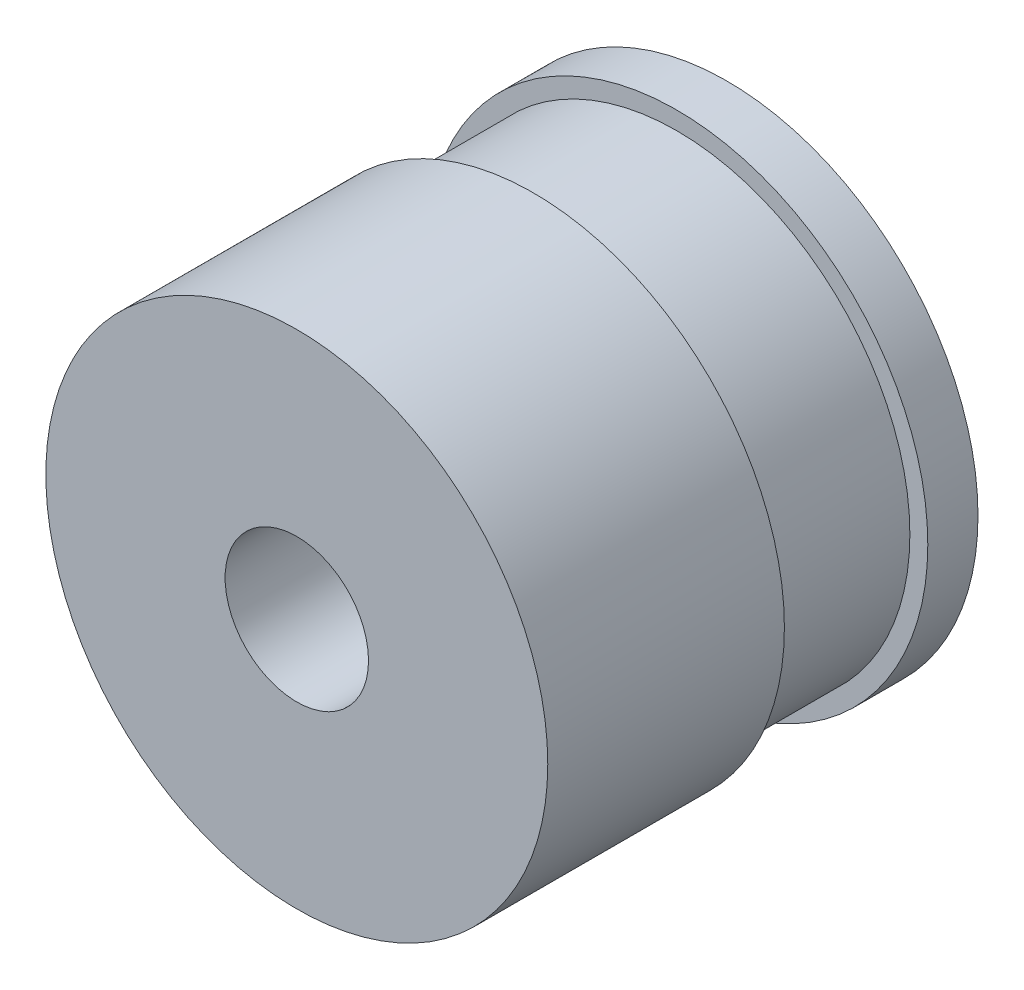
SolidWorks part; units mm, degrees
ref_plane "Plan de face" through (0, 0, 0) normal (0, 0, 1) x (1, 0, 0)
ref_plane "Plan de dessus" through (0, 0, 0) normal (0, 1, 0) x (1, 0, 0)
ref_plane "Plan de droite" through (0, 0, 0) normal (1, 0, 0) x (0, 0, -1)
sketch "Esquisse1" plane through (0, 0, 0) normal (0, 0, 1) x (1, 0, 0)
  circle A0 centre (0, 0) radius 35
  circle A1 centre (0, 0) radius 10
  dimension "D1" = 70
  dimension "D2" = 20
extrude "Boss.-Extru.1" add sketch "Esquisse1" along normal blind 7
sketch "Esquisse2" plane through (0, 0, 7) normal (0, 0, 1) x (1, 0, 0)
  circle A0 centre (0, 0) radius 10
  circle A1 centre (0, 0) radius 32.5
  dimension "D1" = 65
extrude "Boss.-Extru.2" add sketch "Esquisse2" along normal blind 20
sketch "Esquisse3" plane through (0, 0, 27) normal (0, 0, 1) x (1, 0, 0)
  circle A0 centre (0, 0) radius 35
  circle A1 centre (0, 0) radius 10
  dimension "D1" = 70
extrude "Boss.-Extru.3" add sketch "Esquisse3" along normal blind 33
